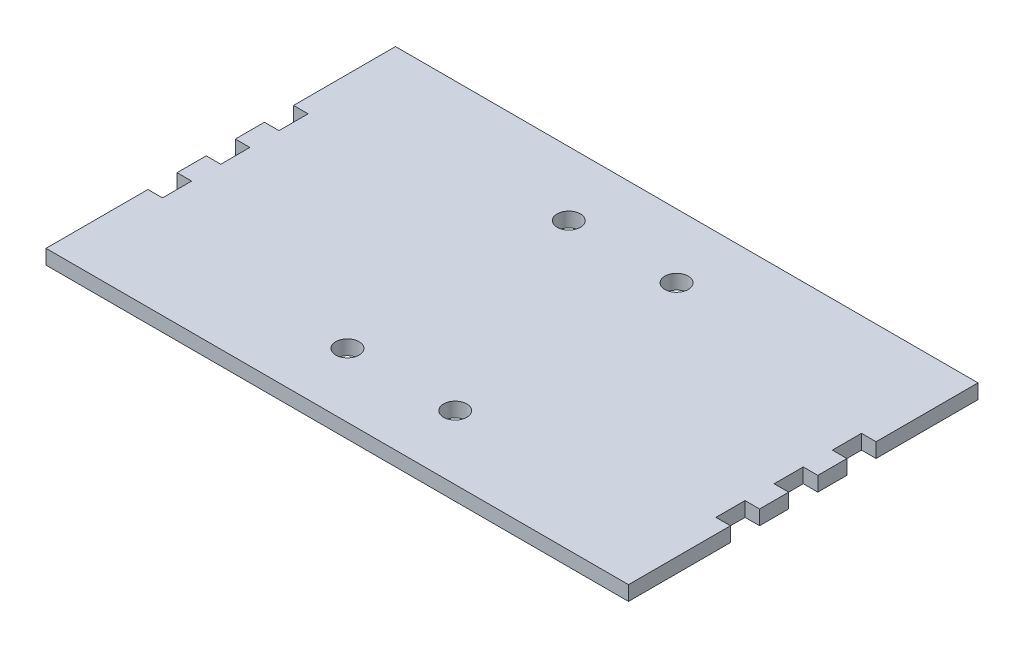
SolidWorks part; units mm, degrees
ref_plane "前视基准面" through (0, 0, 0) normal (0, 0, 1) x (1, 0, 0)
ref_plane "上视基准面" through (0, 0, 0) normal (0, 1, 0) x (1, 0, 0)
ref_plane "右视基准面" through (0, 0, 0) normal (1, 0, 0) x (0, 0, -1)
sketch "草图1" plane through (0, 0, 0) normal (0, 1, 0) x (1, 0, 0)
  line L1 (-100, -60) -> (100, -60)
  line L2 (-100, -60) -> (-100, 60)
  line L3 (-100, 60) -> (100, 60)
  line L4 (100, -60) -> (100, 60)
  line L5 (-100, -60) -> (100, 60) construction
  line L6 (-100, 60) -> (100, -60) construction
  point P0 (0, 0)
  dimension "D1" = 200
  dimension "D2" = 120
extrude "凸台-拉伸1" add sketch "草图1" along normal blind 5
sketch "草图2" plane through (0, 5, 0) normal (0, 1, 0) x (1, 0, 0)
  line L0 (-107.3757, 0) -> (107.3757, 0) construction
  line L1 (100, -60) -> (100, 60) construction
  line L2 (95, -5) -> (100, -5)
  line L3 (95, -5) -> (95, 5)
  line L4 (95, 5) -> (100, 5)
  line L5 (100, -5) -> (100, 5)
  line L6 (95, -5) -> (100, 5) construction
  line L7 (95, 5) -> (100, -5) construction
  line L8 (-100, 60) -> (-100, -60) construction
  line L9 (-95, -5) -> (-100, -5)
  line L10 (-95, -5) -> (-95, 5)
  line L11 (-95, 5) -> (-100, 5)
  line L12 (-100, -5) -> (-100, 5)
  line L13 (-95, -5) -> (-100, 5) construction
  line L14 (-95, 5) -> (-100, -5) construction
  line L16 (-100, -25) -> (-95, -25)
  line L17 (-100, -25) -> (-100, -15)
  line L18 (-100, -15) -> (-95, -15)
  line L19 (-95, -25) -> (-95, -15)
  line L20 (-100, 15) -> (-95, 15)
  line L21 (-100, 15) -> (-100, 25)
  line L22 (-100, 25) -> (-95, 25)
  line L23 (-95, 15) -> (-95, 25)
  line L24 (100, -25) -> (95, -25)
  line L25 (100, -25) -> (100, -15)
  line L26 (100, -15) -> (95, -15)
  line L27 (95, -25) -> (95, -15)
  line L28 (100, 15) -> (95, 15)
  line L29 (100, 15) -> (100, 25)
  line L30 (100, 25) -> (95, 25)
  line L31 (95, 15) -> (95, 25)
  point P0 (97.5, 0)
  point P4 (0, 0)
  point P12 (-97.5, 0)
  dimension "D1" = 10
  dimension "D2" = 5
  dimension "D3" = 10
extrude "切除-拉伸1" cut sketch "草图2" against normal blind 5
sketch "草图3" plane through (0, 5, 0) normal (0, 1, 0) x (1, 0, 0)
  line L0 (0, 0) -> (0, 130.9714) construction
  line L1 (0, 0) -> (-188.6817, 0) construction
  circle A0 centre (-18.5, 38) radius 4
  circle A1 centre (18.5, 38) radius 4
  circle A2 centre (18.5, -38) radius 4
  circle A3 centre (-18.5, -38) radius 4
  dimension "D1" = 76
  dimension "D2" = 37
extrude "切除-拉伸2" cut sketch "草图3" against normal through all
